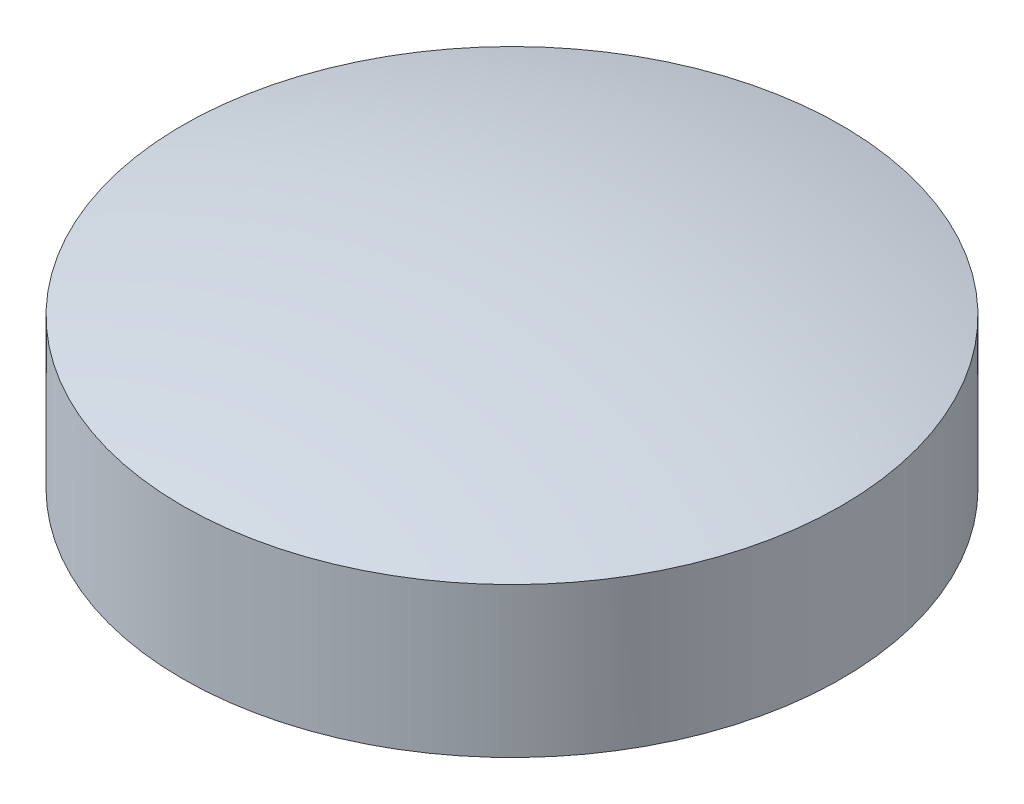
SolidWorks part; units mm, degrees
ref_plane "Front Plane" through (0, 0, 0) normal (0, 0, 1) x (1, 0, 0)
ref_plane "Top Plane" through (0, 0, 0) normal (0, 1, 0) x (1, 0, 0)
ref_plane "Right Plane" through (0, 0, 0) normal (1, 0, 0) x (0, 0, -1)
sketch "Sketch1" plane through (0, 0, 0) normal (0, 0, 1) x (1, 0, 0)
  line L0 (0, 48.7647) -> (0, -63.1218) construction
  line L1 (0, 13) -> (0, 0)
  line L2 (0, 0) -> (22, 0)
  line L3 (22, 0) -> (22, 10)
  line L4 (0, 13) -> (23.5536, 13) construction
  arc A0 (0, 13) -> (22, 10) centre (0, -69.1667) cw
  dimension "D3" = 3
  dimension "D1" = 13
  dimension "D2" = 44
revolve "Revolve1" add sketch "Sketch1" angle 360 about L0
sketch "Sketch2" plane through (0, 0, 0) normal (0, -1, 0) x (1, 0, 0)
  circle A0 centre (-22, 0) radius 1.5
  circle A1 centre (0, 0) radius 22 construction
  dimension "D1" = 3
extrude "Cut-Extrude1" cut sketch "Sketch2" against normal blind 5
